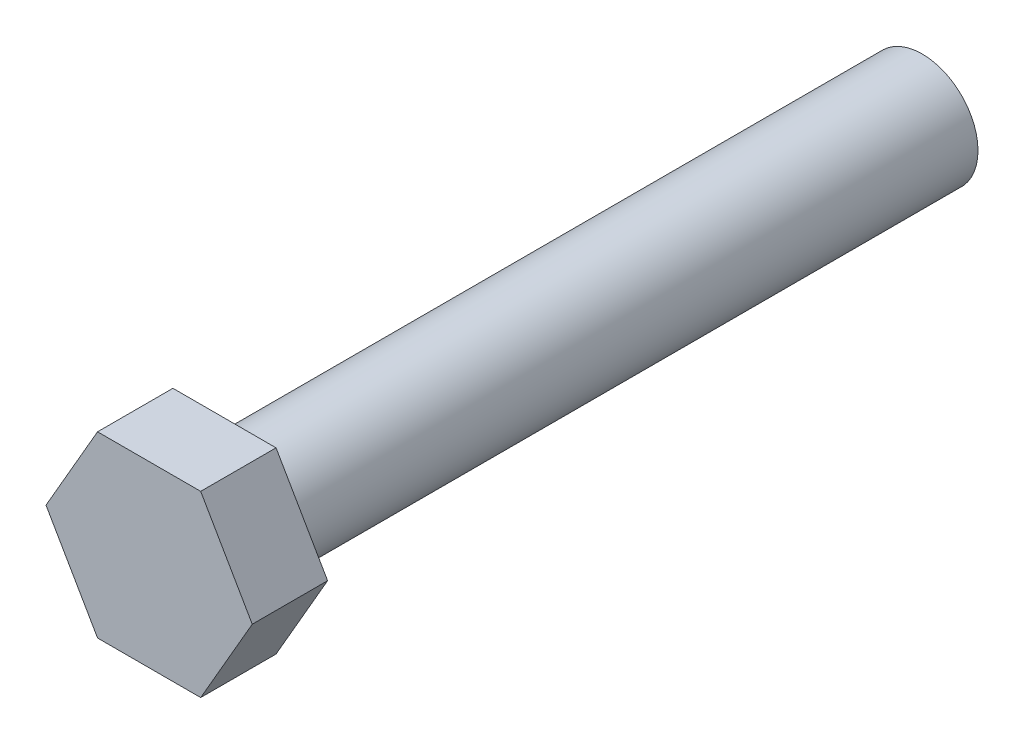
SolidWorks part; units mm, degrees
ref_plane "Front Plane" through (0, 0, 0) normal (0, 0, 1) x (1, 0, 0)
ref_plane "Top Plane" through (0, 0, 0) normal (0, 1, 0) x (1, 0, 0)
ref_plane "Right Plane" through (0, 0, 0) normal (1, 0, 0) x (0, 0, -1)
sketch "Sketch1" plane through (0, 0, 0) normal (0, 0, 1) x (1, 0, 0)
  circle A0 centre (0, 0) radius 4
  dimension "D1" = 8
extrude "Extrude1" add sketch "Sketch1" along normal blind 50
sketch "Sketch2" plane through (0, 0, 50) normal (0, 0, 1) x (1, 0, 0)
  line L1 (7.3901, 0) -> (3.695, 6.4)
  line L2 (3.695, 6.4) -> (-3.695, 6.4)
  line L3 (-3.695, 6.4) -> (-7.3901, 0)
  line L4 (-7.3901, 0) -> (-3.695, -6.4)
  line L5 (-3.695, -6.4) -> (3.695, -6.4)
  line L6 (3.695, -6.4) -> (7.3901, 0)
  circle A0 centre (0, 0) radius 6.4 construction
  dimension "D1" = 12.8
extrude "Extrude2" add sketch "Sketch2" along normal blind 5.4
